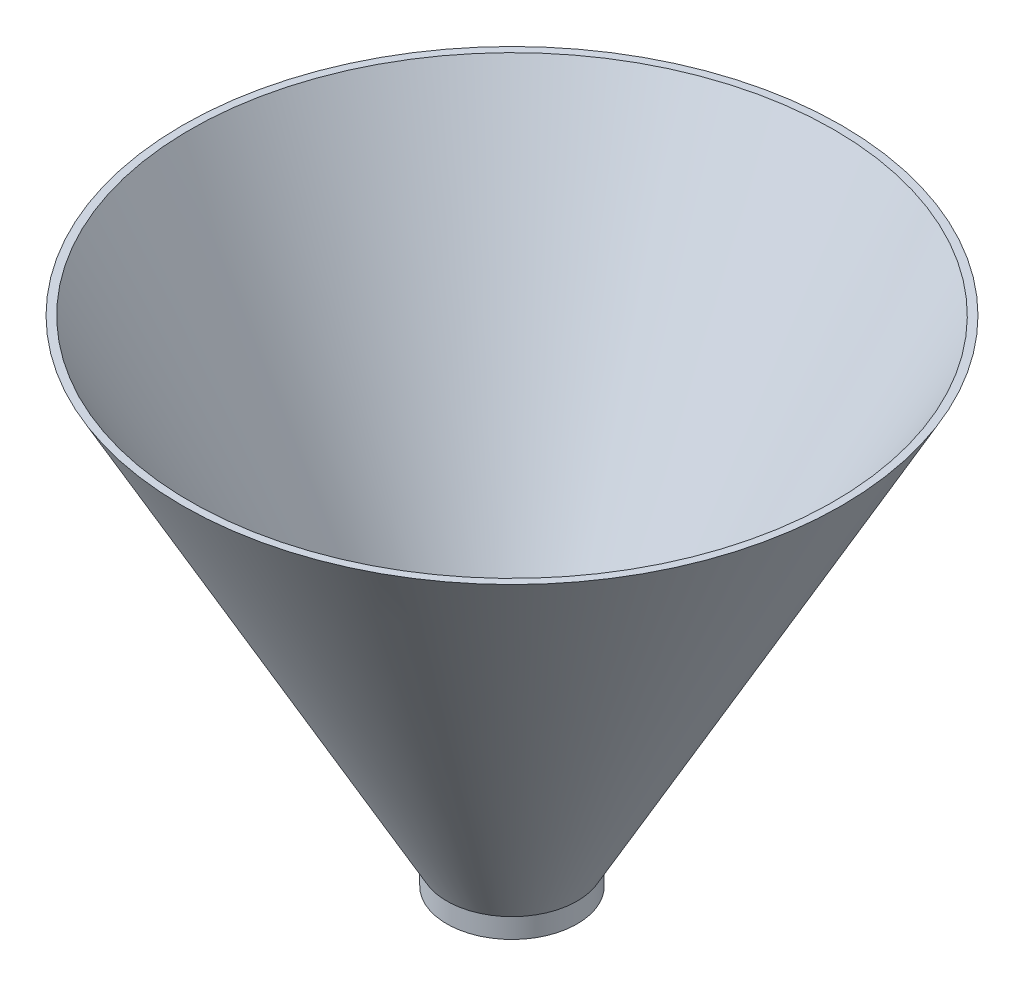
SolidWorks part; units mm, degrees
ref_plane "Front Plane" through (0, 0, 0) normal (0, 0, 1) x (1, 0, 0)
ref_plane "Top Plane" through (0, 0, 0) normal (0, 1, 0) x (1, 0, 0)
ref_plane "Right Plane" through (0, 0, 0) normal (1, 0, 0) x (0, 0, -1)
sketch "Sketch1" plane through (0, 0, 0) normal (1, 0, 0) x (0, 0, -1)
  line L0 (0, 0) -> (0, 75) construction
  line L1 (9.9, 0) -> (9.9, 3)
  line L2 (9.9, 3) -> (50, 75)
  dimension "D1" = 75
  dimension "D2" = 9.9
  dimension "D3" = 50
  dimension "D4" = 3
revolve "Revolve-Thin2" add sketch "Sketch1" angle 360 about L0 wall 1
sketch "Sketch2" plane through (0, 0, 0) normal (1, 0, 0) x (0, 0, -1)
  line L0 (49.1264, 75.4866) -> (-49.1264, 75.4866) construction
  line L1 (-50, 75) -> (50, 75)
  line L2 (-50, 75) -> (-50, 75.4866)
  line L3 (-50, 75.4866) -> (50, 75.4866)
  line L4 (50, 75) -> (50, 75.4866)
extrude "Cut-Extrude1" cut sketch "Sketch2" against normal through all both and the other way through all
